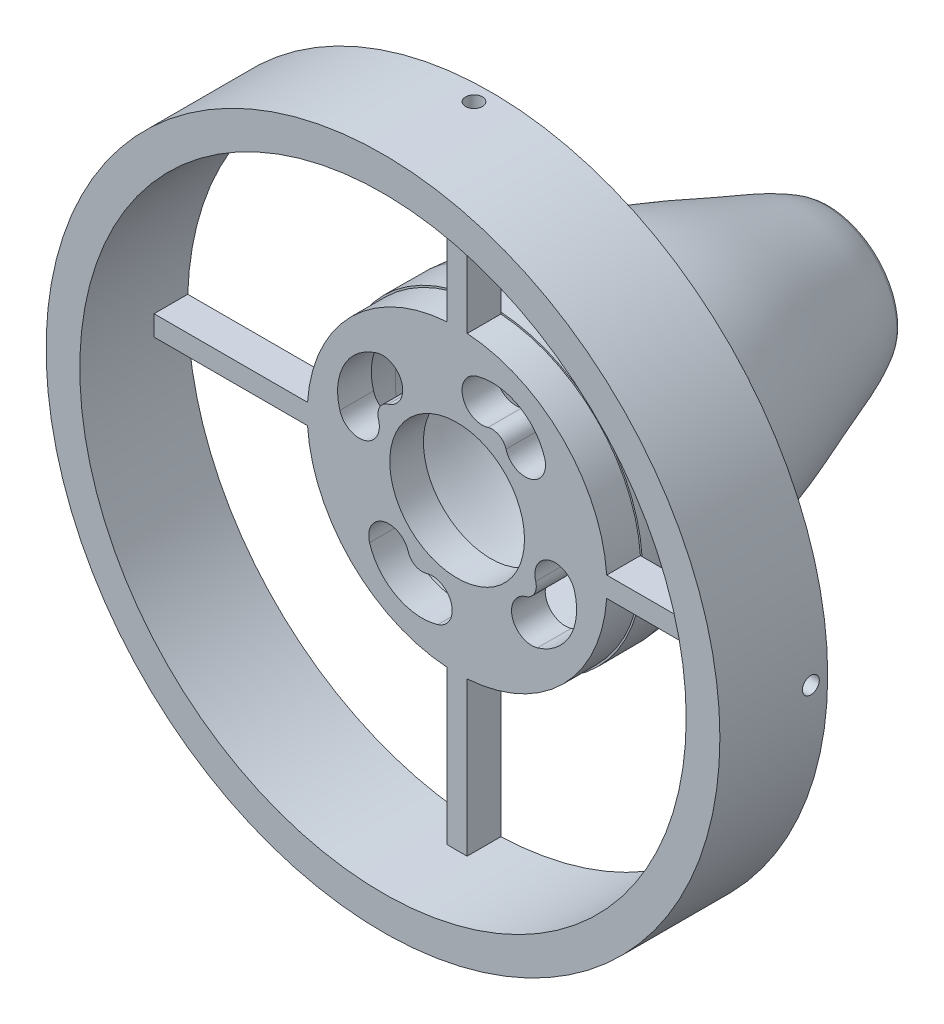
SolidWorks part; units mm, degrees
ref_plane "Front Plane" through (0, 0, 0) normal (0, 0, 1) x (1, 0, 0)
ref_plane "Top Plane" through (0, 0, 0) normal (0, 1, 0) x (1, 0, 0)
ref_plane "Right Plane" through (0, 0, 0) normal (1, 0, 0) x (0, 0, -1)
sketch "Sketch4" plane through (0, 0, 0) normal (0, 0, 1) x (1, 0, 0)
  circle A0 centre (0, 0) radius 50
  circle A1 centre (0, 0) radius 45
  dimension "D1" = 100
  dimension "D2" = 5
extrude "Boss-Extrude2" add sketch "Sketch4" along normal mid plane 5
sketch "Sketch6" plane through (0, 0, 0) normal (0, 0, 1) x (1, 0, 0)
  circle A0 centre (0, 0) radius 22.25
  circle A1 centre (0, 0) radius 10
  dimension "D1" = 44.5
  dimension "D2" = 20
extrude "Boss-Extrude3" add sketch "Sketch6" along normal mid plane 5 separate body
sketch "Sketch7" plane through (0, 0, 0) normal (0, 0, 1) x (1, 0, 0)
  line L0 (0, 0) -> (0, 45) construction
  line L1 (1.5, 22.1737) -> (1.5, 44.975)
  line L2 (-1.5, 22.1737) -> (-1.5, 44.975)
  circle A0 centre (0, 0) radius 45 construction
  arc A1 (1.5, 22.1737) -> (-1.5, 22.1737) centre (0, 0) ccw
  arc A2 (1.5, 44.975) -> (-1.5, 44.975) centre (0, 0) ccw
  dimension "D1" = 3
extrude "Boss-Extrude4" add sketch "Sketch7" along normal mid plane 5
pattern_circular "CirPattern1" count 4 over 360 about axis through (0, 0, 0) along (0, 0, 1) of "Boss-Extrude4"
sketch "Sketch16" plane through (0, 0, 0) normal (1, 0, 0) x (0, 0, -1)
  line L0 (0, 0) -> (2.5, 0) construction
  line L1 (2.5, -50) -> (2.5, 50) construction
  line L2 (2.5, 0) -> (2.5, 20) construction
  line L3 (2.5, 0) -> (52.5, 0) construction
  line L4 (2.5, 20) -> (8.3192, 20)
  line L5 (2.5, 20) -> (2.5, 22.5)
  line L6 (5, 22.5) -> (5, 22.5)
  line L7 (5, 22.5) -> (8.6494, 22.5)
  line L8 (5, 22.5) -> (2.5, 22.5)
  line L9 (8.3192, 20) -> (50.7002, 8.6052) construction
  line L10 (8.6494, 22.5) -> (51.3493, 11.0194) construction
  line L11 (7.5, 22.5) -> (7.5, 22.5)
  line L12 (7.5, 22.5) -> (7.5, 22.5)
  line L13 (7.5, 22.5) -> (8.4646, 22.5)
  line L14 (52.5, 7.3035) -> (52.5, 10.3888)
  line L15 (51.754, 7.843) -> (52.5, 7.3035)
  spline S0 degree 3 poles (8.3192, 20) (11.1233, 19.6727) (15.9732, 19.619) (22.9452, 18.2637) (29.3989, 16.8108) (36.5136, 14.385) (43.6017, 11.5482) (48.6167, 9.8273) (50.7002, 8.6052) knots 0 0 0 0 0.191885 0.327499 0.481339 0.640782 0.837004 1 1 1 1
  spline S1 degree 2 poles (50.7002, 8.6052) (51.2271, 8.2241) (51.754, 7.843) knots 0 0 0 1 1 1
  spline S2 degree 1 poles (8.4646, 22.5) (52.0683, 10.701) knots 0 0 1 1 construction
  spline S3 degree 1 poles (52.0683, 10.701) (53.2191, 9.8687) knots 0 0 1 1 construction
  spline S4 degree 3 poles (8.4646, 22.5) (9.3466, 22.3971) (11.0913, 22.2455) (13.8647, 22.0849) (16.751, 21.8633) (19.671, 21.438) (22.4721, 20.8906) (25.2203, 20.3079) (27.9959, 19.6615) (31.7092, 18.654) (35.3203, 17.4289) (38.8393, 16.1136) (41.441, 15.1132) (44.0158, 14.1235) (46.5874, 13.1937) (48.8683, 12.3196) (50.4761, 11.5709) (51.2833, 11.1479) (51.6801, 10.9266) (51.9154, 10.791) (52.0159, 10.7317) (52.0683, 10.701) knots -0.003294 -0.003294 -0.003294 -0.003294 0.05958 0.122454 0.185328 0.248202 0.311076 0.37395 0.436824 0.499698 0.625446 0.688321 0.751195 0.814069 0.876943 0.939817 0.971254 0.986972 0.994832 0.998761 1.002691 1.002691 1.002691 1.002691
  spline S5 degree 2 poles (52.0683, 10.701) (52.1222, 10.662) (52.2841, 10.5449) (52.5, 10.3888) (52.9135, 10.0897) (53.2191, 9.8687) knots -0.091981 -0.091981 -0.091981 0.010431 0.215256 0.42008 1 1 1 only from (52.0683, 10.701) to (52.5, 10.3888)
  dimension "D1" = 20
  dimension "D2" = 50
  dimension "D3" = 2.5
  dimension "D4" = 2.5
  dimension "D5" = 2.5
revolve "Revolve5" add sketch "Sketch16" angle 360 about L3
sketch "Sketch17" plane through (0, 0, 2.5) normal (0, 0, 1) x (1, 0, 0)
  line L0 (0, 0) -> (35.6042, 0) construction
  line L1 (0, 0) -> (20.0581, 20.0581) construction
  circle A0 centre (0, 0) radius 15 construction
  arc A1 (3.7217, 14.531) -> (10.1236, 11.0685) centre (5.1914, 9.5988) cw construction
  arc A2 (12.9923, 11.9234) -> (2.8668, 17.3997) centre (5.1914, 9.5988) ccw
  arc A3 (7.2549, 10.2137) -> (4.5765, 11.6622) centre (5.1914, 9.5988) ccw
  arc A4 (7.2549, 10.2137) -> (12.9923, 11.9234) centre (10.1236, 11.0685) ccw
  arc A5 (2.8668, 17.3997) -> (4.5765, 11.6622) centre (3.7217, 14.531) ccw
  circle A6 centre (0, 0) radius 15 construction
  arc A7 (14.531, -3.7217) -> (11.0685, -10.1236) centre (9.5988, -5.1914) cw construction
  arc A8 (11.9234, -12.9923) -> (17.3997, -2.8668) centre (9.5988, -5.1914) ccw
  arc A9 (10.2137, -7.2549) -> (11.6622, -4.5765) centre (9.5988, -5.1914) ccw
  arc A10 (10.2137, -7.2549) -> (11.9234, -12.9923) centre (11.0685, -10.1236) ccw
  arc A11 (17.3997, -2.8668) -> (11.6622, -4.5765) centre (14.531, -3.7217) ccw
  circle A12 centre (0, 0) radius 15 construction
  arc A13 (-3.7217, -14.531) -> (-10.1236, -11.0685) centre (-5.1914, -9.5988) cw construction
  arc A14 (-12.9923, -11.9234) -> (-2.8668, -17.3997) centre (-5.1914, -9.5988) ccw
  arc A15 (-7.2549, -10.2137) -> (-4.5765, -11.6622) centre (-5.1914, -9.5988) ccw
  arc A16 (-7.2549, -10.2137) -> (-12.9923, -11.9234) centre (-10.1236, -11.0685) ccw
  arc A17 (-2.8668, -17.3997) -> (-4.5765, -11.6622) centre (-3.7217, -14.531) ccw
  circle A18 centre (0, 0) radius 15 construction
  arc A19 (-14.531, 3.7217) -> (-11.0685, 10.1236) centre (-9.5988, 5.1914) cw construction
  arc A20 (-11.9234, 12.9923) -> (-17.3997, 2.8668) centre (-9.5988, 5.1914) ccw
  arc A21 (-10.2137, 7.2549) -> (-11.6622, 4.5765) centre (-9.5988, 5.1914) ccw
  arc A22 (-10.2137, 7.2549) -> (-11.9234, 12.9923) centre (-11.0685, 10.1236) ccw
  arc A23 (-17.3997, 2.8668) -> (-11.6622, 4.5765) centre (-14.531, 3.7217) ccw
  point P8 (7.6397, 14.1256)
  point P20 (14.1256, -7.6397)
  point P29 (-7.6397, -14.1256)
  point P38 (-14.1256, 7.6397)
  point P43 (0, 0)
  dimension "D1" = 30
  dimension "D2" = 45
extrude "Cut-Extrude2" cut sketch "Sketch17" against normal blind 20
ref_plane "Plane2" through (0, 47.5, 0) normal (0, 1, 0) x (1, 0, 0)
sketch "Sketch19" plane through (0, 47.5, 0) normal (0, 1, 0) x (1, 0, 0)
  line L0 (0, -2.5) -> (0, 2.5)
  line L1 (-50, -2.5) -> (50, -2.5) construction
  line L2 (50, 2.5) -> (-50, 2.5) construction
  circle A0 centre (0, 0) radius 1.25
  dimension "D1" = 2.5
extrude "Cut-Extrude3" cut sketch "Sketch19" along normal mid plane 5 contours A0
pattern_circular "CirPattern2" count 4 over 360 about axis through (0, 0, 0) along (0, 0, 1) of "Cut-Extrude3"
sketch "Sketch20" plane through (0, 0, 2.5) normal (0, 0, 1) x (1, 0, 0)
  circle A0 centre (0, 0) radius 50
  circle A1 centre (0, 0) radius 45
extrude "Boss-Extrude5" add sketch "Sketch20" along normal blind 11
